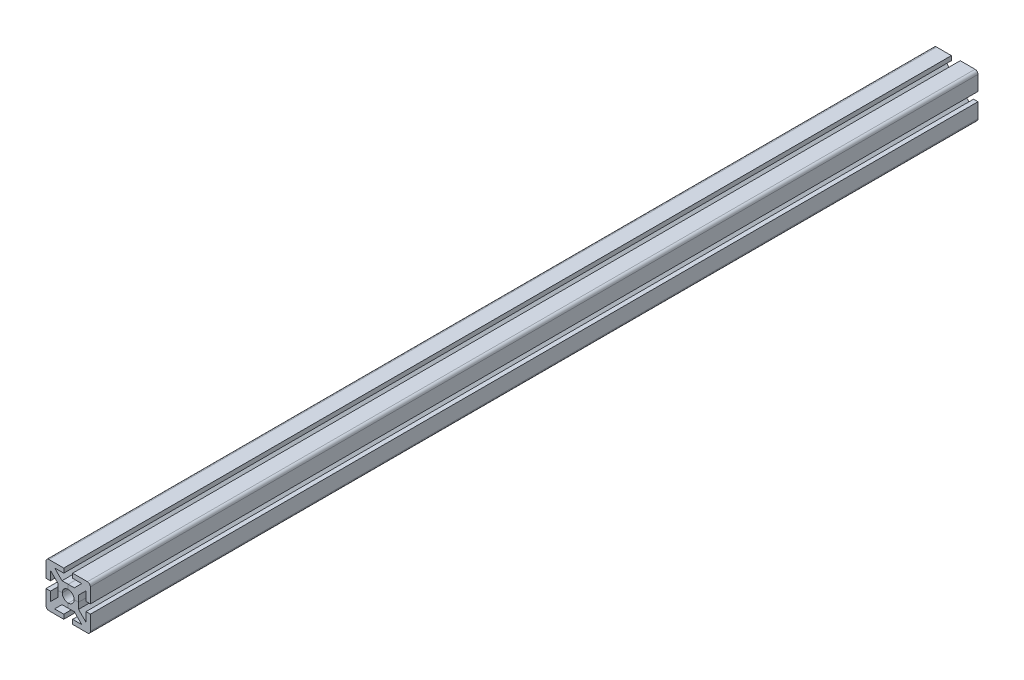
SolidWorks part; units mm, degrees
ref_plane "Alzado" through (0, 0, 0) normal (0, 0, 1) x (1, 0, 0)
ref_plane "Planta" through (0, 0, 0) normal (0, 1, 0) x (1, 0, 0)
ref_plane "Vista lateral" through (0, 0, 0) normal (1, 0, 0) x (0, 0, -1)
sketch "Croquis1" plane through (0, 0, 0) normal (0, 0, 1) x (1, 0, 0)
  line L0 (0, 0) -> (50000, 0) construction
  line L1 (-15, 15) -> (15, 15) construction
  line L2 (-15, 15) -> (-15, -15) construction
  line L3 (-15, -15) -> (15, -15) construction
  line L4 (15, 15) -> (15, -15) construction
  line L5 (-15, 15) -> (15, -15) construction
  line L6 (-15, -15) -> (15, 15) construction
  line L7 (0, 0) -> (0, -50000) construction
  line L8 (0, 4) -> (0, 7)
  line L9 (0, 7) -> (4.1716, 7)
  line L10 (4.1716, 7) -> (9.1716, 12)
  line L11 (9.1716, 12) -> (3, 12)
  line L12 (3, 12) -> (3, 15)
  line L13 (3, 15) -> (15, 15)
  line L20 (2.8284, 2.8284) -> (15, 15)
  arc A0 (2.8284, 2.8284) -> (0, 4) centre (0, 0) ccw
  point P0 (0, 0)
  dimension "D3" = 4
  dimension "D1" = 30
  dimension "D2" = 6
  dimension "D4" = 8
  dimension "D5" = 3
  dimension "D6" = 2
extrude "Saliente-Extruir1" add sketch "Croquis1" along normal mid plane 600
mirror "Simetría1" about plane through (2.8284, 2.8284, 300) normal (-0.7071, 0.7071, 0) of "Saliente-Extruir1"
fillet "Redondeo1" radius 2 1 edges at (15, 15, 0)
pattern_circular "MatrizC4" count 4 over 360 about axis through (0, 0, 0) along (0, 0, 1) of bodies 102
